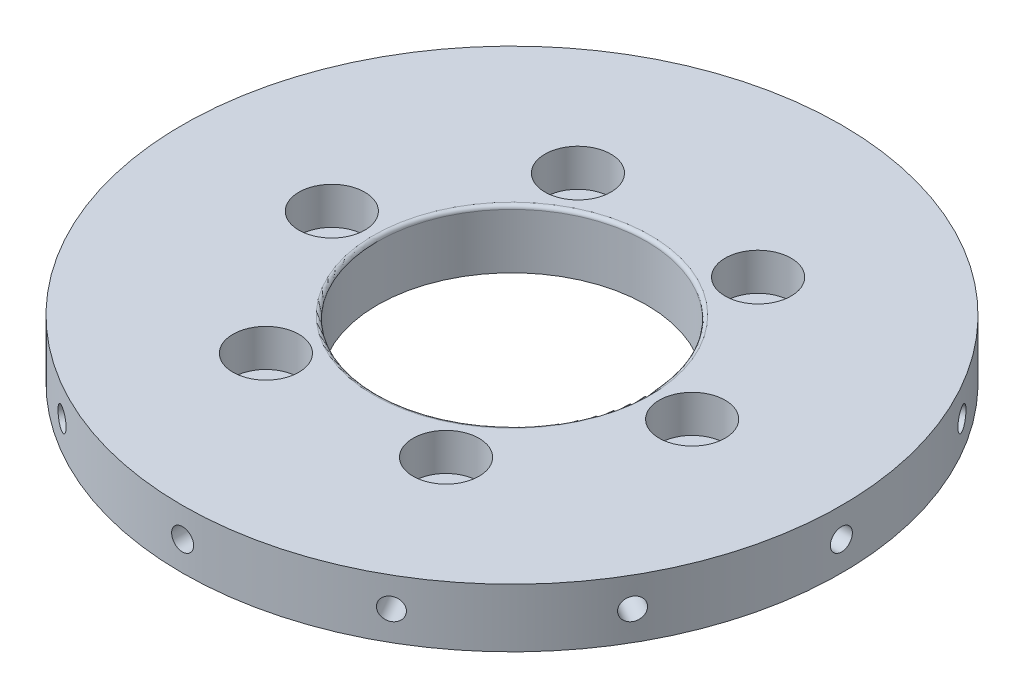
SolidWorks part; units mm, degrees
material "6061 合金"
ref_plane "前视基准面" through (0, 0, 0) normal (0, 0, 1) x (1, 0, 0)
ref_plane "上视基准面" through (0, 0, 0) normal (0, 1, 0) x (1, 0, 0)
ref_plane "右视基准面" through (0, 0, 0) normal (1, 0, 0) x (0, 0, -1)
sketch "草图1" plane through (0, 0, 0) normal (0, 1, 0) x (1, 0, 0)
  circle A0 centre (0, 0) radius 45
  circle A1 centre (0, 0) radius 24.6 construction
  circle A2 centre (-24.6, 0) radius 2.5
  circle A3 centre (-12.3, 21.3042) radius 2.5
  circle A4 centre (12.3, 21.3042) radius 2.5
  circle A5 centre (24.6, 0) radius 2.5
  circle A6 centre (12.3, -21.3042) radius 2.5
  circle A7 centre (-12.3, -21.3042) radius 2.5
  circle A8 centre (0, 0) radius 18.4
  point P19 (0, 0)
  dimension "D1" = 6
  dimension "D2" = 90
extrude "凸台-拉伸1" add sketch "草图1" along normal blind 8
sketch "草图2" plane through (0, 0, 0) normal (0, -1, 0) x (1, 0, 0)
  circle A0 centre (0, 0) radius 24.6 construction
  circle A1 centre (-21.3042, -12.3) radius 4
  circle A2 centre (0, 24.6) radius 4
  circle A3 centre (21.3042, -12.3) radius 4
  point P17 (0, 0)
  dimension "D1" = 3
extrude "切除-拉伸1" cut sketch "草图2" against normal blind 3
sketch "草图4" plane through (0, 8, 0) normal (0, 1, 0) x (1, 0, 0)
  circle A0 centre (-24.6, 0) radius 4.5
  circle A1 centre (0, 0) radius 24.6 construction
  circle A2 centre (-12.3, 21.3042) radius 4.5
  circle A3 centre (12.3, 21.3042) radius 4.5
  circle A4 centre (24.6, 0) radius 4.5
  circle A5 centre (12.3, -21.3042) radius 4.5
  circle A6 centre (-12.3, -21.3042) radius 4.5
  point P16 (0, 0)
  dimension "D1" = 6
extrude "切除-拉伸2" cut sketch "草图4" against normal blind 5.1
ref_plane "基准面1" through (45, 0, 0) normal (1, 0, 0) x (0, 0, -1)
sketch "草图5" plane through (45, 0, 0) normal (1, 0, 0) x (0, 0, -1)
  circle A0 centre (0, 4) radius 1.5
extrude "切除-拉伸3" cut sketch "草图5" against normal blind 10
pattern_circular "阵列(圆周)1" count 12 every 30 about axis through (0, 0, 0) along (0, 1, 0) of "切除-拉伸3"
fillet "圆角1" radius 0.5 1 edges at (0, 8, 18.4)
